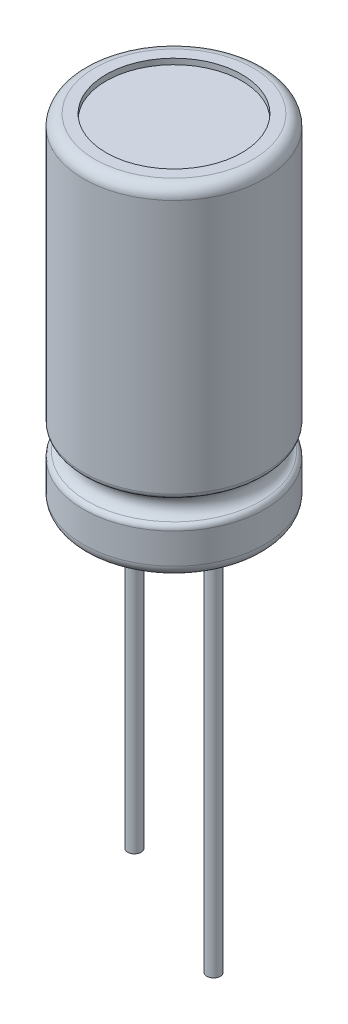
SolidWorks part; units mm, degrees
ref_plane "Front" through (0, 0, 0) normal (0, 0, 1) x (1, 0, 0)
ref_plane "Top" through (0, 0, 0) normal (0, 1, 0) x (1, 0, 0)
ref_plane "Right" through (0, 0, 0) normal (1, 0, 0) x (0, 0, -1)
sketch "Sketch1" plane through (0, 0, 0) normal (0, 1, 0) x (1, 0, 0)
  circle A0 centre (0, 0) radius 4
  dimension "D1" = 8
extrude "Base-Extrude" add sketch "Sketch1" along normal blind 15
sketch "Sketch2" plane through (0, 0, 0) normal (1, 0, 0) x (0, 0, -1)
  line L0 (-4, 15) -> (-4, 0) construction
  line L1 (-4, 3.0532) -> (-4, 2.0532)
  line L2 (0, 0) -> (0, 7.7627) construction
  line L3 (0, 15) -> (0, 0) construction
  arc A0 (-4, 2.0532) -> (-4, 3.0532) centre (-4, 2.5532) ccw
  dimension "D1" = 0.5
revolve "Cut-Revolve1" cut sketch "Sketch2" angle 360 about L2
fillet "Fillet1" radius 0.5 2 edges at (0, 0, 4) (0, 15, 4)
fillet "Fillet2" radius 0.25 2 edges at (0, 2.0532, -4) (0, 3.0532, -4)
sketch "Sketch4" plane through (0, 0, 0) normal (0, -1, 0) x (1, 0, 0)
  circle A0 centre (0, 0) radius 3
  dimension "D1" = 6
extrude "Cut-Extrude1" cut sketch "Sketch4" against normal blind 0.25
sketch "Sketch3" plane through (0, 0.25, 0) normal (0, -1, 0) x (1, 0, 0)
  circle A0 centre (-1.75, 0) radius 0.3
  circle A1 centre (1.75, 0) radius 0.3
  dimension "D1" = 0.6
  dimension "D2" = 1.75
  dimension "D3" = 3.5
extrude "Boss-Extrude1" add sketch "Sketch3" along normal blind 17.25
sketch "Sketch5" plane through (0, -17, 0) normal (0, -1, 0) x (1, 0, 0)
  circle A1 centre (-1.75, 0) radius 0.3
  circle A2 centre (-1.75, 0) radius 0.3
  dimension "D1" = 0
extrude "Cut-Extrude2" cut sketch "Sketch5" against normal blind 3
sketch "Sketch6" plane through (0, 15, 0) normal (0, 1, 0) x (-1, 0, 0)
  circle A0 centre (0, 0) radius 3
  dimension "D1" = 6
extrude "Cut-Extrude3" cut sketch "Sketch6" against normal blind 0.25
